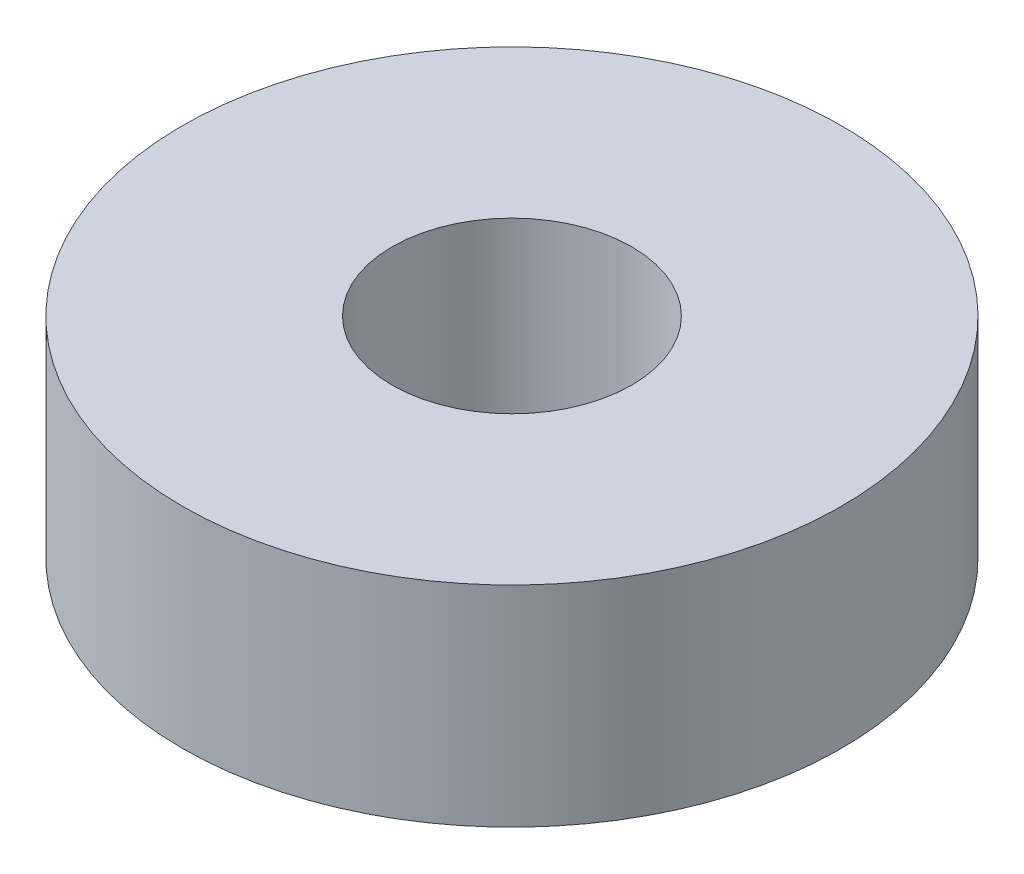
SolidWorks part; units mm, degrees
ref_plane "Front Plane" through (0, 0, 0) normal (0, 0, 1) x (1, 0, 0)
ref_plane "Top Plane" through (0, 0, 0) normal (0, 1, 0) x (1, 0, 0)
ref_plane "Right Plane" through (0, 0, 0) normal (1, 0, 0) x (0, 0, -1)
sketch "Croquis1" plane through (0, 0, 0) normal (0, 1, 0) x (1, 0, 0)
  circle A0 centre (0, 0) radius 11
  circle A1 centre (0, 0) radius 4
  dimension "D1" = 22
  dimension "D2" = 8
extrude "Saliente-Extruir1" add sketch "Croquis1" along normal blind 7
